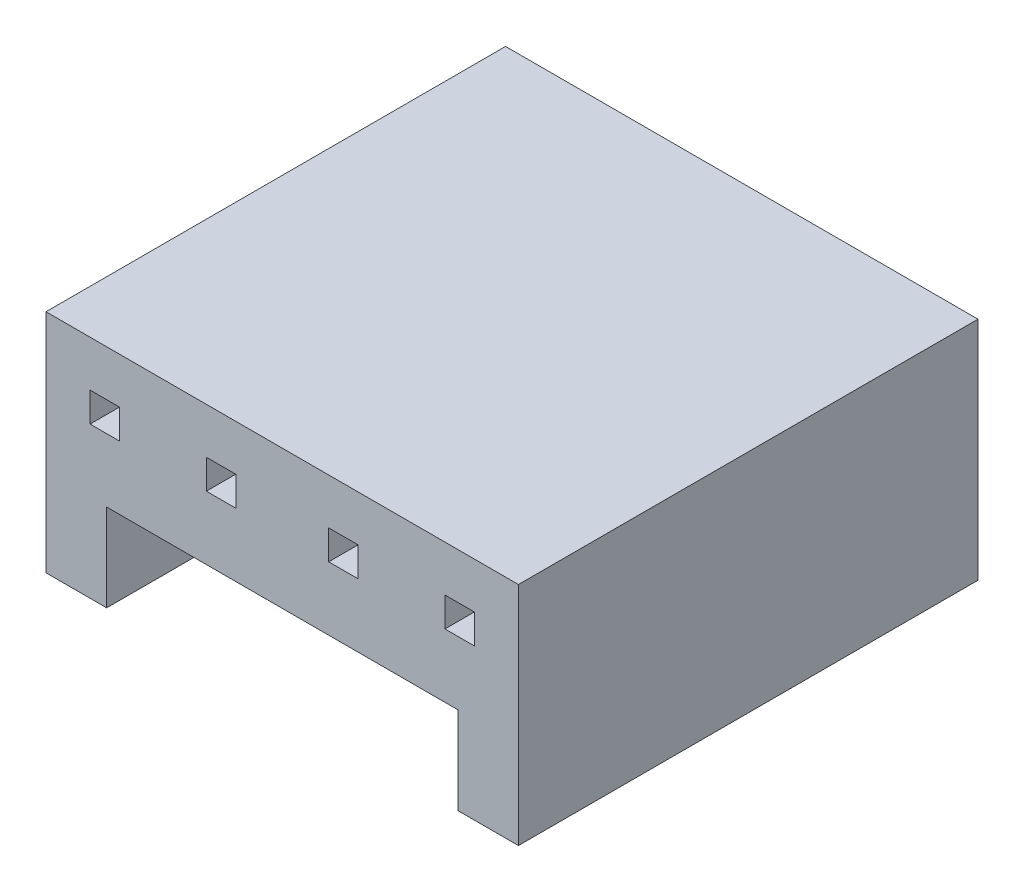
SolidWorks part; units mm, degrees
ref_plane "Front Plane" through (0, 0, 0) normal (0, 0, 1) x (1, 0, 0)
ref_plane "Top Plane" through (0, 0, 0) normal (0, 1, 0) x (1, 0, 0)
ref_plane "Right Plane" through (0, 0, 0) normal (1, 0, 0) x (0, 0, -1)
sketch "Sketch1" plane through (0, 0, 0) normal (0, 0, 1) x (1, 0, 0)
  line L0 (0, 4.92) -> (10.28, 4.92)
  line L2 (0, 0) -> (0, 4.92)
  line L5 (0, 0) -> (1.32, 0)
  line L6 (1.32, 0) -> (1.32, 1.9)
  line L7 (1.32, 1.9) -> (8.96, 1.9)
  line L10 (6.151, 3.9228) -> (6.791, 3.9228)
  line L11 (0.959, 3.9228) -> (0.959, 3.2828)
  line L12 (0.959, 3.2828) -> (1.599, 3.2828)
  line L13 (0.959, 3.9228) -> (1.599, 3.9228)
  line L14 (1.599, 3.9228) -> (1.599, 3.2828)
  line L15 (6.151, 3.2828) -> (6.151, 3.9228)
  line L16 (3.489, 3.9228) -> (3.489, 3.2828)
  line L17 (3.489, 3.2828) -> (4.129, 3.2828)
  line L18 (4.129, 3.2828) -> (4.129, 3.9228)
  line L19 (4.129, 3.9228) -> (3.489, 3.9228)
  line L20 (6.791, 3.2828) -> (6.151, 3.2828)
  line L21 (6.791, 3.9228) -> (6.791, 3.2828)
  line L22 (8.681, 3.9228) -> (8.681, 3.2828)
  line L23 (9.321, 3.9228) -> (8.681, 3.9228)
  line L24 (9.321, 3.2828) -> (8.681, 3.2828)
  line L25 (9.321, 3.9228) -> (9.321, 3.2828)
  line L26 (8.96, 0) -> (8.96, 1.9)
  line L27 (10.28, 0) -> (8.96, 0)
  line L28 (10.28, 0) -> (10.28, 4.92)
  point P3 (6.151, 3.6028)
  dimension "D1" = 4.92
  dimension "D2" = 0.64
  dimension "D3" = 0.64
  dimension "D4" = 0.959
  dimension "D5" = 0.9972
  dimension "D6" = 1.9
  dimension "D7" = 7.64
  dimension "D8" = 1.32
  dimension "D9" = 4.92
  dimension "D10" = 0.959
  dimension "D11" = 0.9972
  dimension "D12" = 1.3828
  dimension "D13" = 1.89
  dimension "D14" = 2.0221
  dimension "D15" = 1.89
  dimension "D16" = 0.64
  dimension "D17" = 1.3828
  dimension "D18" = 0.9972
  dimension "D19" = 1.32
  dimension "D20" = 1.599
  dimension "D21" = 0.64
  dimension "D22" = 0.64
  dimension "D23" = 2.809
  dimension "D24" = 2.0228
extrude "Boss-Extrude1" add sketch "Sketch1" against normal blind 10
